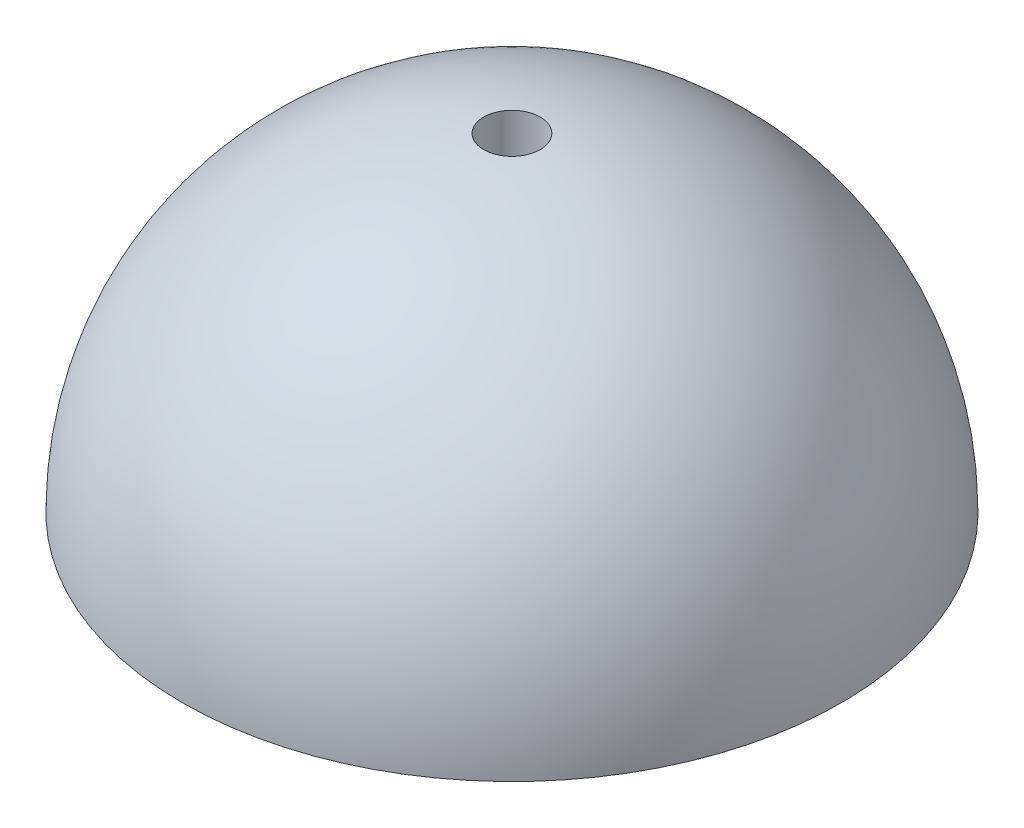
SolidWorks part; units mm, degrees
ref_plane "Plan de face" through (0, 0, 0) normal (0, 0, 1) x (1, 0, 0)
ref_plane "Plan de dessus" through (0, 0, 0) normal (0, 1, 0) x (1, 0, 0)
ref_plane "Plan de droite" through (0, 0, 0) normal (1, 0, 0) x (0, 0, -1)
sketch "Esquisse1" plane through (0, 0, 0) normal (0, 0, 1) x (1, 0, 0)
  line L0 (0, 0) -> (17.5, 0)
  line L1 (-1.5, 17.5) -> (1.5, 17.5)
  line L2 (-1.5, 17.5) -> (-1.5, -17.5)
  line L3 (-1.5, -17.5) -> (1.5, -17.5)
  line L4 (1.5, 17.5) -> (1.5, -17.5)
  line L5 (-1.5, 17.5) -> (1.5, -17.5) construction
  line L6 (-1.5, -17.5) -> (1.5, 17.5) construction
  line L7 (17.5, 0) -> (0, 0)
  line L8 (0, 0) -> (-17.5, 0)
  line L9 (0, 17.5) -> (0, -17.5)
  circle A0 centre (0, 0) radius 17.5
  point P8 (0, 17.5)
  dimension "D1" = 35
  dimension "D2" = 3
revolve "Révolution1" add sketch "Esquisse1" angle 360 about L9
